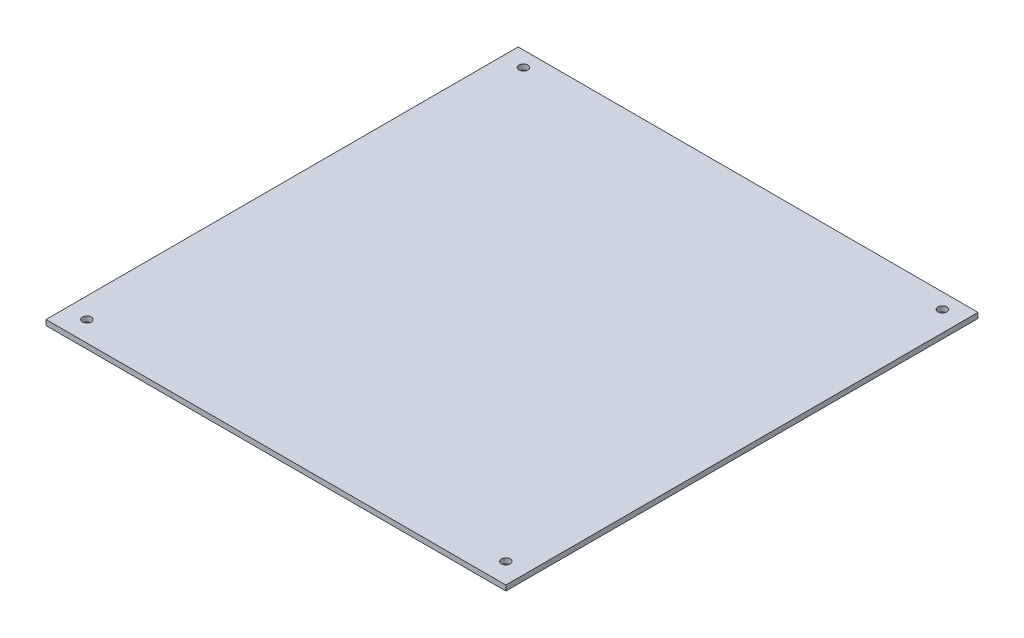
SolidWorks part; units mm, degrees
ref_plane "Front Plane" through (0, 0, 0) normal (0, 0, 1) x (1, 0, 0)
ref_plane "Top Plane" through (0, 0, 0) normal (0, 1, 0) x (1, 0, 0)
ref_plane "Right Plane" through (0, 0, 0) normal (1, 0, 0) x (0, 0, -1)
sketch "Sketch1" plane through (0, 0, 0) normal (0, 1, 0) x (1, 0, 0)
  line L1 (131, -134.5) -> (-131, -134.5)
  line L2 (131, -134.5) -> (131, 134.5)
  line L3 (131, 134.5) -> (-131, 134.5)
  line L4 (-131, -134.5) -> (-131, 134.5)
  line L5 (131, -134.5) -> (-131, 134.5) construction
  line L6 (131, 134.5) -> (-131, -134.5) construction
  circle A0 centre (119.34, -122.84) radius 2.5
  circle A1 centre (-119.34, -122.84) radius 2.5
  circle A2 centre (-119.34, 125.84) radius 2.5
  circle A3 centre (119.34, 125.84) radius 2.5
  point P0 (0, 0)
  dimension "D3" = 11.66
  dimension "D4" = 11.66
  dimension "D5" = 5
  dimension "D7" = 11.66
  dimension "D1" = 269
  dimension "D2" = 262
  dimension "D6" = 8.66
extrude "Boss-Extrude1" add sketch "Sketch1" along normal blind 3
